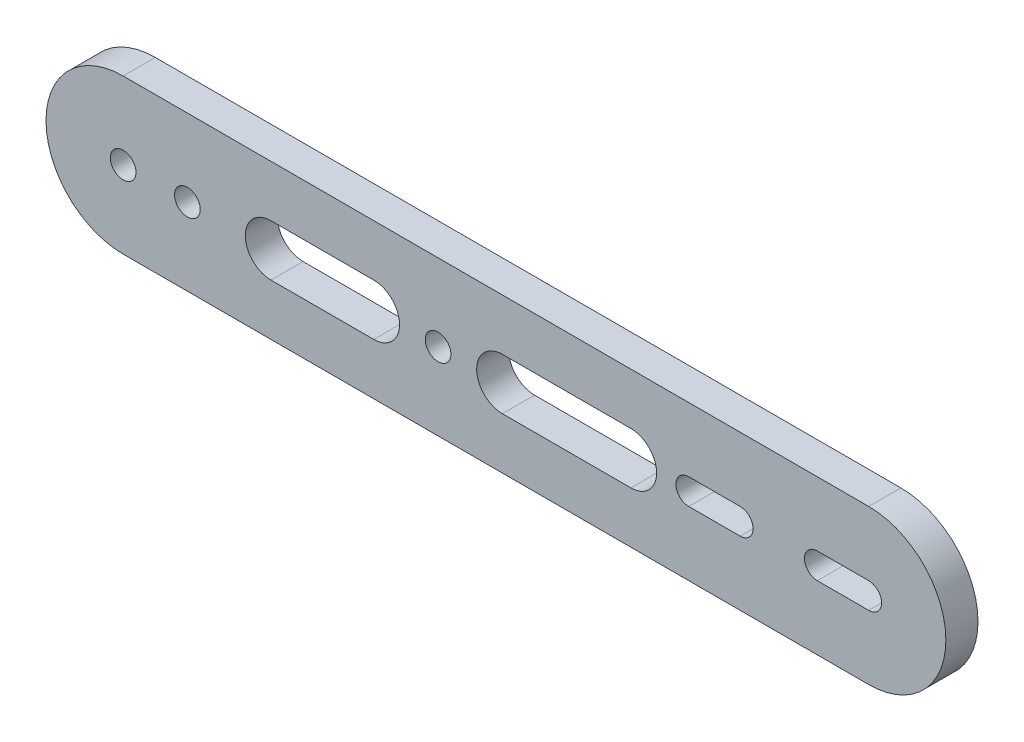
SolidWorks part; units mm, degrees
material "Thornel Mat VMA"
ref_plane "前视基准面" through (0, 0, 0) normal (0, 0, 1) x (1, 0, 0)
ref_plane "上视基准面" through (0, 0, 0) normal (0, 1, 0) x (1, 0, 0)
ref_plane "右视基准面" through (0, 0, 0) normal (1, 0, 0) x (0, 0, -1)
sketch "草图1" plane through (0, 0, 0) normal (0, 0, 1) x (1, 0, 0)
  line L0 (0, 0) -> (116, 0) construction
  line L1 (0, 12) -> (116, 12)
  line L2 (0, -12) -> (116, -12)
  line L3 (23, 0) -> (39, 0) construction
  line L4 (23, 4) -> (39, 4)
  line L5 (23, -4) -> (39, -4)
  line L6 (59, 0) -> (79, 0) construction
  line L7 (59, 4) -> (79, 4)
  line L8 (59, -4) -> (79, -4)
  arc A0 (0, 12) -> (0, -12) centre (0, 0) ccw
  arc A1 (116, -12) -> (116, 12) centre (116, 0) ccw
  circle A2 centre (49, 0) radius 2
  circle A3 centre (0, 0) radius 2
  circle A5 centre (10, 0) radius 2
  arc A6 (23, 4) -> (23, -4) centre (23, 0) ccw
  arc A7 (39, -4) -> (39, 4) centre (39, 0) ccw
  arc A8 (59, 4) -> (59, -4) centre (59, 0) ccw
  arc A9 (79, -4) -> (79, 4) centre (79, 0) ccw
  point P3 (58, 0)
  point P16 (31, 0)
  point P23 (69, 0)
  line B0 (108, 2) -> (116, 2)
  arc B1 (116, -2) -> (116, 2) centre (116, 0) ccw
  line B2 (108, -2) -> (116, -2)
  arc B3 (108, 2) -> (108, -2) centre (108, 0) ccw
  line B4 (88, 2) -> (96, 2)
  arc B5 (96, -2) -> (96, 2) centre (96, 0) ccw
  line B6 (88, -2) -> (96, -2)
  arc B7 (88, 2) -> (88, -2) centre (88, 0) ccw
  dimension "D1" = 12
  dimension "D2" = 4
  dimension "D3" = 4
  dimension "D4" = 4
  dimension "D7" = 10
  dimension "D9" = 16
  dimension "D8" = 4
  dimension "D13" = 4
  dimension "D5" = 49
  dimension "D6" = 116
  dimension "D10" = 10
  dimension "D11" = 20
  dimension "D12" = 10
sketch_block_instance "块1-1"
sketch_block "块1" parameters "D1"=2, "D3"=2, "D2"=8, "D4"=12, "D5"=8
extrude "凸台-拉伸1" add sketch "草图1" along normal blind 5
